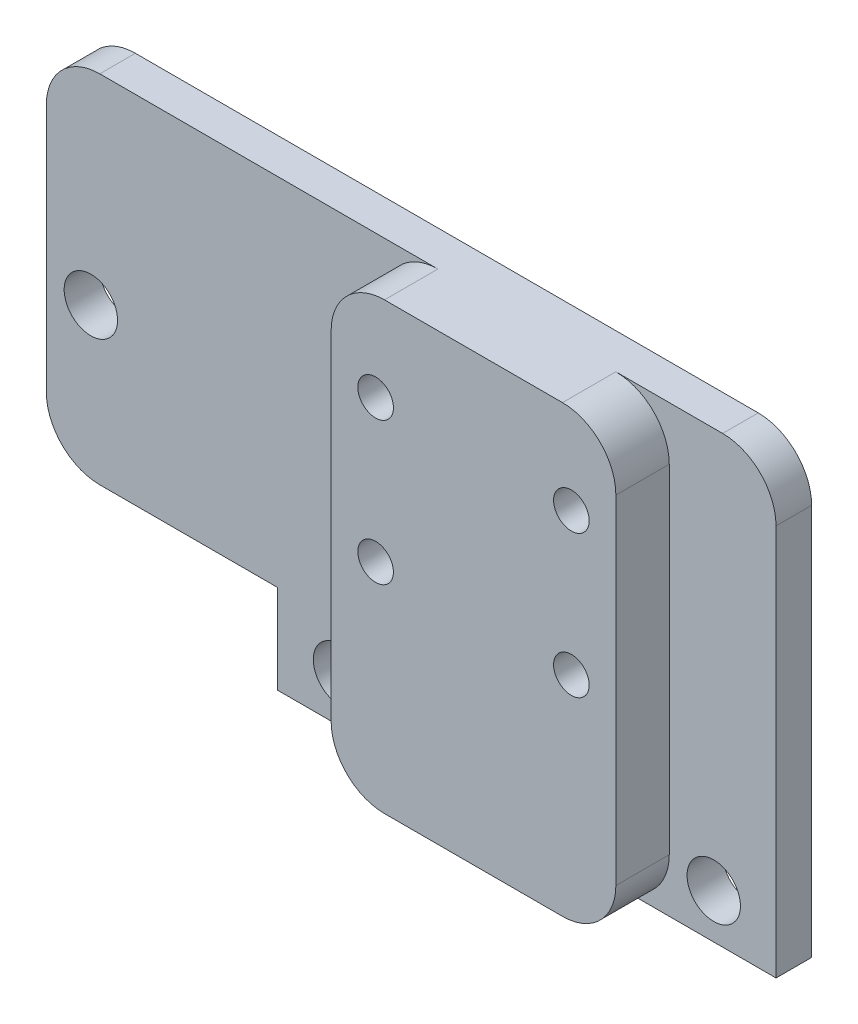
SolidWorks part; units mm, degrees
ref_plane "Plan de face" through (0, 0, 0) normal (0, 0, 1) x (1, 0, 0)
ref_plane "Plan de dessus" through (0, 0, 0) normal (0, 1, 0) x (1, 0, 0)
ref_plane "Plan de droite" through (0, 0, 0) normal (1, 0, 0) x (0, 0, -1)
sketch "Esquisse1" plane through (0, 0, 0) normal (0, 0, 1) x (1, 0, 0)
  line L0 (0, 0) -> (0, 40.5421) construction
  line L1 (-27, 25) -> (27, 25)
  line L2 (27, 25) -> (27, 5)
  line L3 (27, 5) -> (14, 5)
  line L4 (14, 5) -> (14, 0)
  line L5 (14, 0) -> (-14, 0)
  line L6 (-14, 0) -> (-14, 5)
  line L7 (-14, 5) -> (-27, 5)
  line L8 (-27, 5) -> (-27, 25)
  point P5 (0, 25)
  point P13 (0, 0)
  dimension "D1" = 5
  dimension "D2" = 54
  dimension "D3" = 28
  dimension "D4" = 20
extrude "Boss.-Extru.1" add sketch "Esquisse1" along normal blind 2
sketch "Esquisse2" plane through (0, 0, 2) normal (0, 0, 1) x (1, 0, 0)
  line L0 (27, 25) -> (-27, 25) construction
  line L1 (-8, 25) -> (8, 25)
  line L2 (-8, 25) -> (-8, 0)
  line L3 (-8, 0) -> (8, 0)
  line L4 (8, 25) -> (8, 0)
  line L6 (-14, 0) -> (14, 0) construction
  point P6 (0, 0)
  dimension "D1" = 16
extrude "Boss.-Extru.2" add sketch "Esquisse2" along normal blind 3
sketch "Esquisse3" plane through (0, 0, 2) normal (0, 0, 1) x (1, 0, 0)
  line L0 (-14, 5) -> (-14, 0) construction
  line L2 (-14, 0) -> (-8, 0) construction
  line L3 (14, 0) -> (14, 5) construction
  line L5 (-27, 5) -> (-14, 5) construction
  line L6 (-27, 25) -> (-27, 5) construction
  circle A0 centre (-24.5, 13.5) radius 1.5
  circle A1 centre (-10.5, 2.5) radius 1.5
  circle A2 centre (10.5, 2.5) radius 1.5
  dimension "D1" = 3
  dimension "D2" = 3.5
  dimension "D3" = 2.5
  dimension "D4" = 3.5
  dimension "D5" = 8.5
  dimension "D6" = 2.5
extrude "Enlèv. mat.-Extru.1" cut sketch "Esquisse3" against normal up to next
sketch "Esquisse4" plane through (0, 0, 5) normal (0, 0, 1) x (1, 0, 0)
  line L0 (5.5, 20) -> (-5.5, 20) construction
  line L1 (8, 25) -> (-8, 25) construction
  circle A0 centre (-5.5, 20) radius 1
  circle A1 centre (-5.5, 12) radius 1
  circle A2 centre (5.5, 12) radius 1
  circle A3 centre (5.5, 20) radius 1
  point P8 (0, 20)
  dimension "D1" = 2
  dimension "D2" = 11
  dimension "D3" = 8
  dimension "D4" = 5
extrude "Enlèv. mat.-Extru.2" cut sketch "Esquisse4" against normal up to next
sketch "Esquisse5" plane through (0, 0, 2) normal (0, 0, 1) x (1, 0, 0)
  line L1 (27, 25) -> (14, 25)
  line L2 (27, 25) -> (27, 5)
  line L3 (27, 5) -> (14, 5)
  line L4 (14, 25) -> (14, 5)
extrude "Enlèv. mat.-Extru.3" cut sketch "Esquisse5" against normal up to next
fillet "Congé1" radius 3 7 edges at (-27, 5, 1) (-27, 25, 1) (14, 25, 1)
